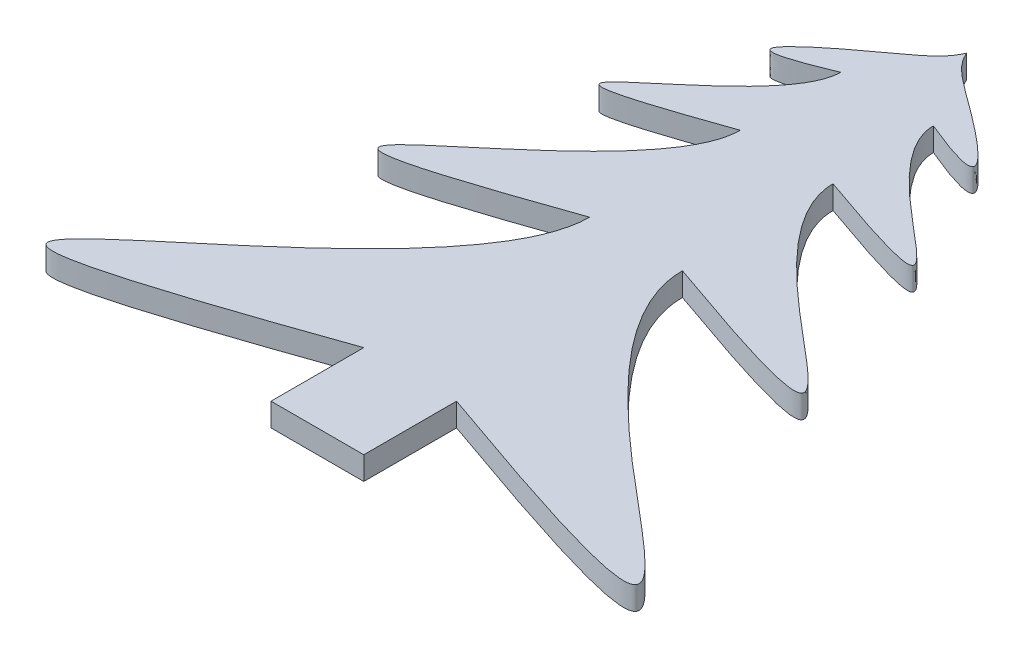
SolidWorks part; units mm, degrees
ref_plane "Front Plane" through (0, 0, 0) normal (0, 0, 1) x (1, 0, 0)
ref_plane "Top Plane" through (0, 0, 0) normal (0, 1, 0) x (1, 0, 0)
ref_plane "Right Plane" through (0, 0, 0) normal (1, 0, 0) x (0, 0, -1)
sketch "Sketch1" plane through (0, 0, 0) normal (0, 1, 0) x (1, 0, 0)
  line L0 (0, 0) -> (0, 101.6) construction
  line L1 (-6.35, 12.7) -> (6.35, 12.7)
  line L2 (-6.35, 12.7) -> (-6.35, 25.4)
  line L4 (6.35, 12.7) -> (6.35, 25.4)
  spline S0 degree 3 poles (0, 101.6) (0.8591, 99.5016) (8.0467, 94.5428) (20.6251, 84.6846) (6.35, 90.6931) knots 0 0 0 0 0.277088 1 1 1 1
  spline S1 degree 3 poles (6.35, 90.6931) (6.3423, 80.561) (40.4862, 64.8592) (6.35, 76.9472) knots 0 0 0 0 1 1 1 1
  spline S2 degree 3 poles (6.35, 76.9472) (6.3385, 61.7491) (57.5544, 38.1963) (6.35, 56.3283) knots 0 0 0 0 1 1 1 1
  spline S3 degree 3 poles (6.35, 56.3283) (6.3328, 33.5312) (83.1565, -1.7981) (6.35, 25.4) knots 0 0 0 0 1 1 1 1
  spline S4 degree 3 poles (-6.35, 56.3283) (-6.3328, 33.5312) (-83.1565, -1.7981) (-6.35, 25.4) knots 0 0 0 0 1 1 1 1
  spline S5 degree 3 poles (-6.35, 76.9472) (-6.3385, 61.7491) (-57.5544, 38.1963) (-6.35, 56.3283) knots 0 0 0 0 1 1 1 1
  spline S6 degree 3 poles (-6.35, 90.6931) (-6.3423, 80.561) (-40.4862, 64.8592) (-6.35, 76.9472) knots 0 0 0 0 1 1 1 1
  spline S7 degree 3 poles (0, 101.6) (-0.8591, 99.5016) (-8.0467, 94.5428) (-20.6251, 84.6846) (-6.35, 90.6931) knots 0 0 0 0 0.277088 1 1 1 1
  dimension "D1" = 12.7
  dimension "D3" = 12.7
  dimension "D4" = 101.6
extrude "Boss-Extrude1" add sketch "Sketch1" against normal blind 3.175
